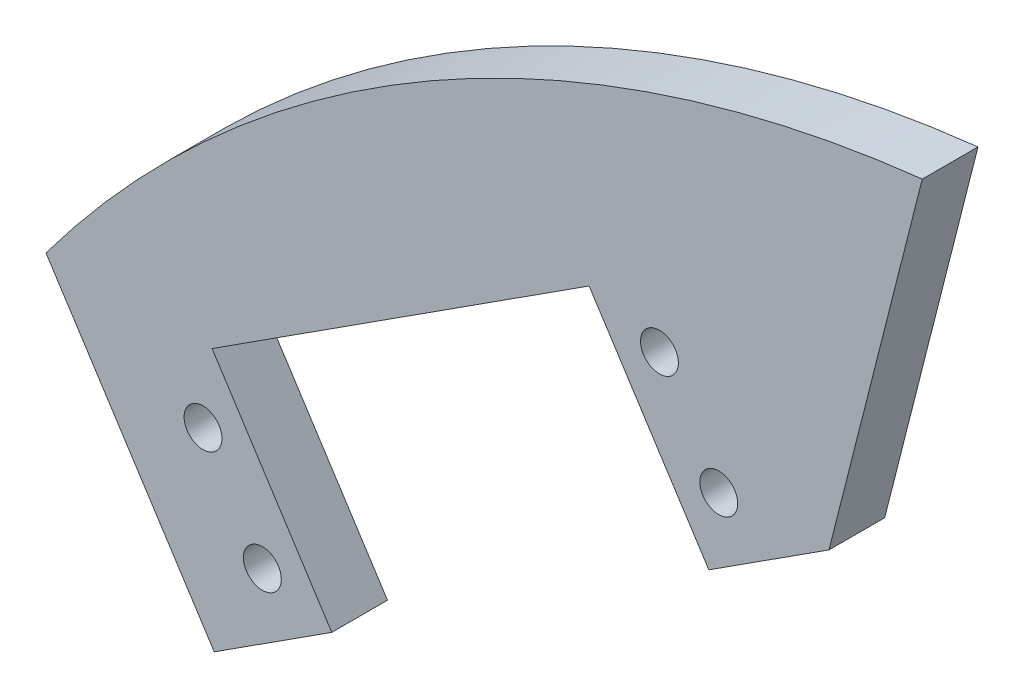
SolidWorks part; units mm, degrees
ref_plane "Front Plane" through (0, 0, 0) normal (0, 0, 1) x (1, 0, 0)
ref_plane "Top Plane" through (0, 0, 0) normal (0, 1, 0) x (1, 0, 0)
ref_plane "Right Plane" through (0, 0, 0) normal (1, 0, 0) x (0, 0, -1)
sketch "Sketch1" plane through (0, 0, 0) normal (0, 0, 1) x (1, 0, 0)
  line L0 (-15.3435, 23.8386) -> (0, 0)
  line L1 (0, 0) -> (56.0656, 36.0861)
  line L2 (56.0656, 36.0861) -> (64.5738, 69.629)
  arc A1 (64.5738, 69.629) -> (-15.3435, 23.8386) centre (77.2789, -45.1795) ccw
  dimension "D5" = 115.5093
  dimension "D1" = 66.675
  dimension "D2" = 137
  dimension "D3" = 28.3497
  dimension "D4" = 34.6051
extrude "Boss-Extrude1" add sketch "Sketch1" along normal blind 5.08
sketch "Sketch2" plane through (0, 0, 5.08) normal (0, 0, 1) x (1, 0, 0)
  line L0 (0, 0) -> (56.0656, 36.0861) construction
  line L5 (22.4945, 26.3828) -> (27.9123, 17.9655) construction
  line L7 (-15.3435, 23.8386) -> (0, 0) construction
  line L13 (27.9934, 17.8395) -> (16.9957, 34.9261) construction
  line L14 (10.7999, 6.7731) -> (45.1868, 28.9059)
  line L19 (40.6001, 43.9825) -> (46.0124, 35.5737) construction
  line L20 (-1.0233, 17.1919) -> (4.3889, 8.7831) construction
  line L24 (43.3063, 39.7781) -> (1.6828, 12.9875) construction
  line L30 (10.7999, 6.7731) -> (-0.1978, 23.8597)
  line L31 (-0.1978, 23.8597) -> (34.1891, 45.9925)
  line L32 (45.1868, 28.9059) -> (34.1891, 45.9925)
  circle A7 centre (46.0124, 35.5737) radius 1.7272
  circle A9 centre (-1.0233, 17.1919) radius 1.7272
  circle A10 centre (4.3889, 8.7831) radius 1.7272
  circle A11 centre (40.6001, 43.9825) radius 1.7272
  point P0 (14.4221, 21.1871)
  dimension "D2" = 10
  dimension "D3" = 10.0101
  dimension "D5" = 3.4544
  dimension "D6" = 15.15
  dimension "D1" = 49.5
  dimension "D4" = 33.1942
  dimension "D7" = 20.32
  dimension "D8" = 40.894
extrude "Cut-Extrude1" cut sketch "Sketch2" against normal up to surface (5.08 mm away) up to face at (25.1336, 34.466, 0)
